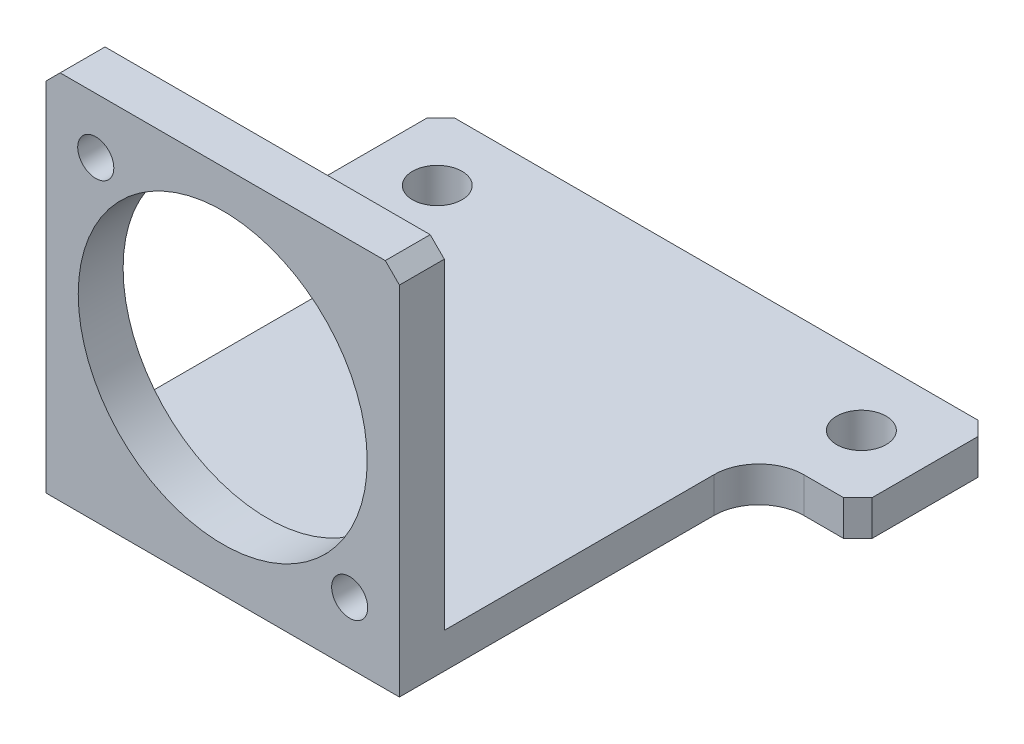
SolidWorks part; units mm, degrees
material "PVC Rigid"
ref_plane "Front Plane" through (0, 0, 0) normal (0, 0, 1) x (1, 0, 0)
ref_plane "Top Plane" through (0, 0, 0) normal (0, 1, 0) x (1, 0, 0)
ref_plane "Right Plane" through (0, 0, 0) normal (1, 0, 0) x (0, 0, -1)
other "PLA"
sketch "Sketch1" plane through (0, 0, 0) normal (0, 0, 1) x (1, 0, 0)
  line L0 (0, 26.24) -> (0, 0.415) construction
  line L1 (-25, -26.24) -> (25, -26.24)
  line L2 (-25, -26.24) -> (-25, 26.24)
  line L3 (-25, 26.24) -> (25, 26.24)
  line L4 (25, -26.24) -> (25, 26.24)
  line L5 (-25, -26.24) -> (25, 26.24) construction
  line L6 (-25, 26.24) -> (25, -26.24) construction
  line L7 (0, 0.415) -> (-25, 0.415) construction
  circle A1 centre (0, 0.415) radius 20.44
  point P0 (0, 0)
  dimension "D3" = 40.88
  dimension "D4" = 25.825
  dimension "D1" = 50
  dimension "D2" = 52.48
extrude "Boss-Extrude1" add sketch "Sketch1" along normal blind 6.35
sketch "Sketch4" plane through (0, -26.24, 0) normal (0, -1, 0) x (1, 0, 0)
  line L0 (25, 0) -> (25, -63.5)
  line L1 (25, -63.5) -> (-25, -63.5)
  line L2 (-25, -63.5) -> (-25, 0)
  line L3 (-25, -63.5) -> (-39, -63.5)
  line L4 (-25, 0) -> (25, 0)
  line L5 (25, 0) -> (25, 6.35)
  line L6 (25, 6.35) -> (-25, 6.35)
  line L7 (-25, 6.35) -> (-25, 0)
  line L8 (-25, 0) -> (25, 0)
  line L9 (25, 0) -> (25, 6.35)
  line L10 (25, 6.35) -> (-25, 6.35)
  line L11 (-25, 6.35) -> (-25, 0)
  line L12 (-39, -63.5) -> (-39, -44.5)
  line L13 (-39, -44.5) -> (-25, -44.5)
  line L14 (25, -44.5) -> (39, -44.5)
  line L15 (39, -44.5) -> (39, -63.5)
  line L16 (39, -63.5) -> (25, -63.5)
  line L17 (-30, -54) -> (30, -54) construction
  line L18 (0, 0) -> (0, -54) construction
  circle A0 centre (-30, -54) radius 3.5
  circle A1 centre (30, -54) radius 3.5
  line M6 (-25, 0) -> (25, 0)
  dimension "D5" = 7
  dimension "D6" = 54
  dimension "D4" = 6
  dimension "D2" = 6
  dimension "D3" = 14
  dimension "D8" = 60
  dimension "D1" = 0
extrude "Boss-Extrude4" add sketch "Sketch4" against normal blind 5 contours L2 L1 L0 M6 | L13 L12 L3 L2 A0 | L16 L15 L14 L0 A1 | L17 L2 L1 L0
sketch "Sketch6" plane through (0, 0, 6.35) normal (0, 0, 1) x (1, 0, 0)
  line L0 (0, 20.855) -> (0, 0.415) construction
  line L1 (0, 0.415) -> (-17.9605, 18.3755) construction
  line L2 (0, 0.415) -> (17.9605, -17.5455) construction
  line L4 (25, -26.24) -> (25, 26.24)
  line L5 (25, 26.24) -> (-25, 26.24)
  line L6 (-25, 26.24) -> (-25, -26.24)
  line L7 (-25, -26.24) -> (25, -26.24)
  line L8 (25, -26.24) -> (25, 26.24)
  line L9 (25, 26.24) -> (-25, 26.24)
  line L10 (-25, 26.24) -> (-25, -26.24)
  line L11 (-25, -26.24) -> (25, -26.24)
  circle A0 centre (0, 0.415) radius 25.4
  circle A1 centre (0, 0.415) radius 20.44 construction
  circle A2 centre (0, 0.415) radius 20.44 construction
  circle A13 centre (-17.9605, 18.3755) radius 1.8397 construction
  circle A14 centre (17.9605, -17.5455) radius 2.6097 construction
  dimension "D2" = 50.8
  dimension "D3" = 45
  dimension "D1" = 0
hole_wizard "#10 Clearance Hole1" positions "Sketch7" profile "Sketch8" hole size "#10" standard "ANSI Inch" end condition up to next
sketch "Sketch7" plane through (0, 0, 6.35) normal (0, 0, 1) x (1, 0, 0)
  line L8 (25, -26.24) -> (25, 26.24)
  line L9 (25, 26.24) -> (-25, 26.24)
  line L10 (-25, 26.24) -> (-25, -26.24)
  line L11 (-25, -26.24) -> (25, -26.24)
  line L12 (25, -26.24) -> (25, 26.24)
  line L13 (25, 26.24) -> (-25, 26.24)
  line L14 (-25, 26.24) -> (-25, -26.24)
  line L15 (-25, -26.24) -> (25, -26.24)
  point P17 (-17.9605, 18.3755)
  point P20 (17.9605, -17.5455)
  dimension "D1" = 0
sketch "Sketch8" plane through (17.9605, -17.5455, 6.35) normal (1, 0, 0) x (0, -1, 0)
  line L0 (0, 0) -> (0, 6.35)
  line L1 (0, 6.35) -> (2.5527, 6.35)
  line L2 (2.5527, 6.35) -> (2.5527, 0)
  line L5 (2.5527, 0) -> (0, 0)
  line L11 (0, -6.35) -> (0, 107.95) construction
  dimension "Thru Hole Dia." = 5.1054
  dimension "Thru Hole Depth" = 6.35
fillet "Fillet1" radius 6.35 2 edges at (25, -23.74, -44.5) (-25, -23.74, -44.5)
chamfer "Chamfer1" distance 2 angle 45 4 edges at (-39, -23.74, -63.5) (-39, -23.74, -44.5) (39, -23.74, -63.5) (39, -23.74, -44.5)
chamfer "Chamfer2" distance 2 angle 45 2 edges at (25, 26.24, 3.175) (-25, 26.24, 3.175)
